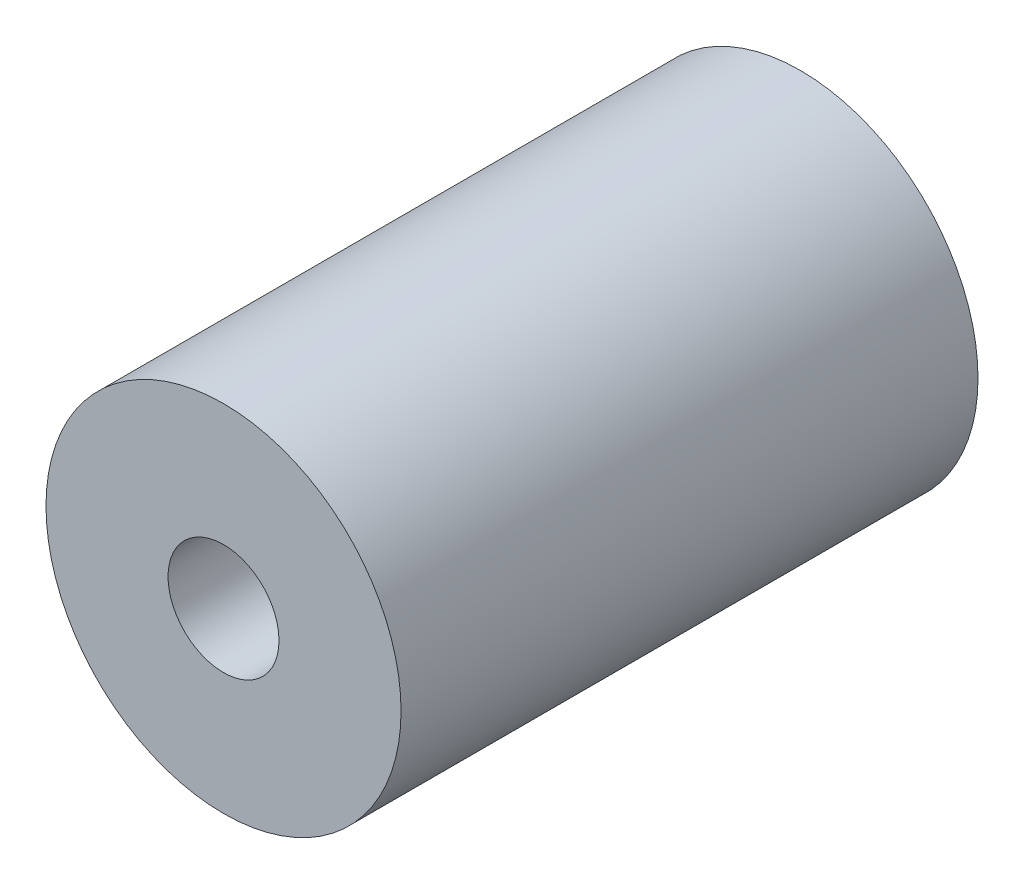
SolidWorks part; units mm, degrees
material "Malleable Cast Iron"
ref_plane "Front Plane" through (0, 0, 0) normal (0, 0, 1) x (1, 0, 0)
ref_plane "Top Plane" through (0, 0, 0) normal (0, 1, 0) x (1, 0, 0)
ref_plane "Right Plane" through (0, 0, 0) normal (1, 0, 0) x (0, 0, -1)
sketch "Sketch1" plane through (0, 0, 0) normal (0, 0, 1) x (1, 0, 0)
  circle A0 centre (0, 0) radius 8
  circle A1 centre (0, 0) radius 2.5
  dimension "D1" = 16
  dimension "D2" = 5
extrude "Boss-Extrude1" add sketch "Sketch1" along normal blind 26
